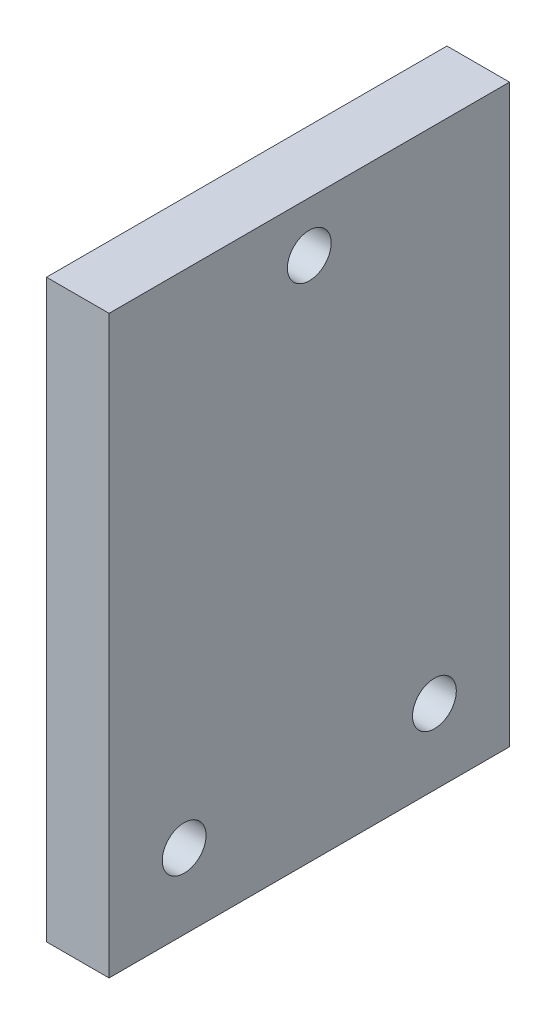
SolidWorks part; units mm, degrees
ref_plane "Front Plane" through (0, 0, 0) normal (0, 0, 1) x (1, 0, 0)
ref_plane "Top Plane" through (0, 0, 0) normal (0, 1, 0) x (1, 0, 0)
ref_plane "Right Plane" through (0, 0, 0) normal (1, 0, 0) x (0, 0, -1)
sketch "Sketch1" plane through (0, 0, 0) normal (0, 1, 0) x (1, 0, 0)
  line L1 (0, 0) -> (55, 0)
  line L2 (0, 0) -> (0, 32)
  line L3 (0, 32) -> (55, 32)
  line L4 (55, 0) -> (55, 32)
  dimension "D1" = 32
  dimension "D2" = 55
extrude "Boss-Extrude1" add sketch "Sketch1" along normal blind 46
sketch "Sketch2" plane through (0, 0, 0) normal (0, -1, 0) x (1, 0, 0)
  line L0 (0, 0) -> (55, 0) construction
  line L1 (5, 0) -> (50, 0)
  line L2 (5, 0) -> (5, -32)
  line L3 (5, -32) -> (50, -32)
  line L4 (50, 0) -> (50, -32)
  line L5 (55, -32) -> (0, -32) construction
  line L6 (0, -32) -> (0, 0) construction
  line L7 (55, 0) -> (55, -32) construction
  dimension "D1" = 5
  dimension "D2" = 5
extrude "Cut-Extrude1" cut sketch "Sketch2" against normal blind 45
sketch "Sketch3" plane through (0, 46, 0) normal (0, 1, 0) x (1, 0, 0)
  line L0 (55, 32) -> (0, 32) construction
  line L1 (55, 0) -> (55, 32) construction
  circle A0 centre (43.5, 26) radius 1.75
  circle A1 centre (43.5, 6) radius 1.75
  circle A2 centre (11.5, 26) radius 1.75
  circle A3 centre (11.5, 6) radius 1.75
  dimension "D1" = 3.5
  dimension "D2" = 20
  dimension "D3" = 20
  dimension "D4" = 32
  dimension "D5" = 32
  dimension "D6" = 6
  dimension "D7" = 11.5
extrude "Cut-Extrude2" cut sketch "Sketch3" against normal through all
sketch "Sketch4" plane through (55, 0, 0) normal (1, 0, 0) x (0, 0, -1)
  line L0 (0, 46) -> (32, 46) construction
  line L1 (0, 46) -> (0, 0) construction
  circle A0 centre (6, 6) radius 1.75
  circle A1 centre (26, 6) radius 1.75
  circle A2 centre (16, 42) radius 1.75
  dimension "D1" = 3.5
  dimension "D2" = 3.5
  dimension "D6" = 3.5
  dimension "D3" = 20
  dimension "D4" = 40
  dimension "D5" = 6
  dimension "D7" = 4
  dimension "D8" = 16
extrude "Cut-Extrude3" cut sketch "Sketch4" against normal through all
sketch "Sketch7" plane through (0, 0, 0) normal (-1, 0, 0) x (0, 0, 1)
  line L0 (-32, 46) -> (-32, 0) construction
  line L1 (-32, 0) -> (0, 0)
  line L2 (-32, 0) -> (-32, 46)
  line L3 (-32, 46) -> (0, 46)
  line L4 (0, 0) -> (0, 46)
  line L5 (-32, 0) -> (0, 0) construction
extrude "Cut-Extrude5" cut sketch "Sketch7" against normal blind 50
